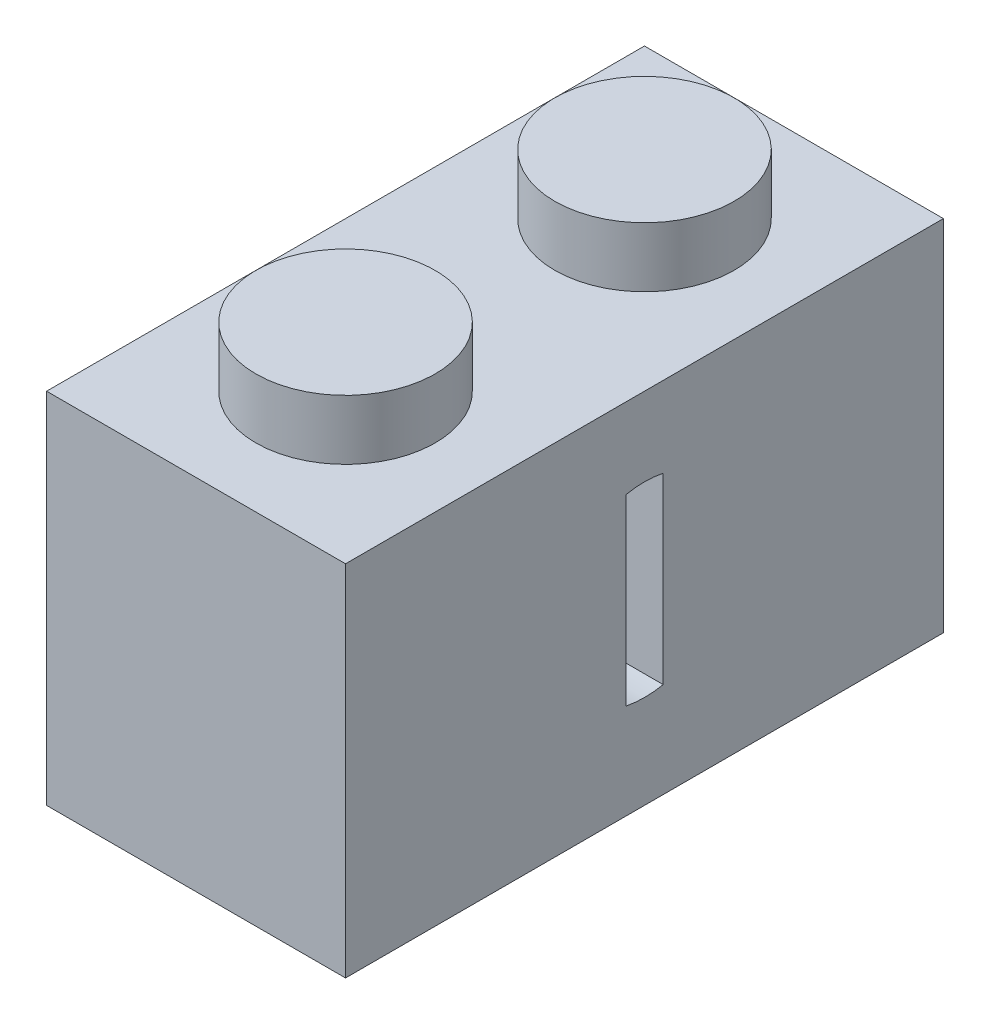
SolidWorks part; units mm, degrees
ref_plane "Front Plane" through (0, 0, 0) normal (0, 0, 1) x (1, 0, 0)
ref_plane "Top Plane" through (0, 0, 0) normal (0, 1, 0) x (1, 0, 0)
ref_plane "Right Plane" through (0, 0, 0) normal (1, 0, 0) x (0, 0, -1)
sketch "Sketch1" plane through (0, 0, 0) normal (0, 0, 1) x (1, 0, 0)
  line L1 (0, 9.6) -> (8, 9.6)
  line L2 (0, 9.6) -> (0, 0)
  line L3 (0, 0) -> (8, 0)
  line L4 (8, 9.6) -> (8, 0)
  dimension "D1" = 8
  dimension "D2" = 9.6
extrude "Boss-Extrude1" add sketch "Sketch1" along normal blind 16 contours L2 L1 L4 L3
sketch "Sketch4" plane through (0, 0, 0) normal (0, -1, 0) x (1, 0, 0)
  line L0 (1.6, 14.4) -> (1.6, 1.6)
  line L1 (1.6, 1.6) -> (6.4, 1.6)
  line L2 (6.4, 1.6) -> (6.4, 14.4)
  line L3 (6.4, 14.4) -> (1.6, 14.4)
  line L4 (0, 0) -> (8, 0)
  line L5 (8, 0) -> (8, 16)
  line L6 (8, 16) -> (0, 16)
  line L7 (0, 16) -> (0, 0)
  line L8 (0, 0) -> (8, 0)
  line L9 (8, 0) -> (8, 16)
  line L10 (8, 16) -> (0, 16)
  line L11 (0, 16) -> (0, 0)
  dimension "D1" = 0
  dimension "D2" = 1.6
extrude "Cut-Extrude1" cut sketch "Sketch4" against normal offset from surface (8 mm away) 8 contours L1 L2 L3 L0 up to face at (4, 0, 8)
sketch "Sketch5" plane through (0, 9.6, 0) normal (0, 1, 0) x (1, 0, 0)
  line L0 (4, -12) -> (4, -16) construction
  line L1 (0, -16) -> (8, -16) construction
  line L2 (4, -4) -> (4, 0) construction
  line L3 (0, 0) -> (8, 0) construction
  line L4 (0, -16) -> (0, 0) construction
  circle A0 centre (4, -12) radius 2.4
  circle A1 centre (4, -4) radius 2.4
  dimension "D1" = 4.8
  dimension "D2" = 0
  dimension "D3" = 8
extrude "Boss-Extrude2" add sketch "Sketch5" along normal blind 1.6 contours A0 | A1
sketch "Sketch6" plane through (6.4, 0, 0) normal (-1, 0, 0) x (0, 0, 1)
  line L0 (1.6, 5) -> (8, 5) construction
  line L1 (8, 5) -> (14.4, 5) construction
  line L4 (1.6, 8) -> (1.6, 0)
  line L5 (1.6, 0) -> (14.4, 0)
  line L6 (14.4, 0) -> (14.4, 8)
  line L7 (14.4, 8) -> (1.6, 8)
  line L8 (1.6, 8) -> (1.6, 0)
  line L9 (1.6, 0) -> (14.4, 0)
  line L10 (14.4, 0) -> (14.4, 8)
  line L11 (14.4, 8) -> (1.6, 8) construction
  circle A0 centre (8, 5) radius 3.5
  line M11 (14.4, 8) -> (1.6, 8)
  dimension "D2" = 7
  dimension "D3" = 3
  dimension "D1" = 0
extrude "Boss-Extrude3" add sketch "Sketch6" along normal up to surface (4.8 mm away) contours A0 M11 up to face at (1.6, 4, 8)
sketch "Sketch7" plane through (0, 0, 0) normal (-1, 0, 0) x (0, 0, 1)
  arc A0 (6.1972, 8) -> (9.8028, 8) centre (8, 5) ccw construction
  arc A1 (6.1972, 8) -> (9.8028, 8) centre (8, 5) ccw
  circle A2 centre (8, 5) radius 2.5
  dimension "D1" = 5
extrude "Cut-Extrude2" cut sketch "Sketch7" against normal blind 3.5 contours A2
sketch "Sketch8" plane through (3.5, 0, 0) normal (-1, 0, 0) x (0, 0, 1)
  line L0 (7.5, 7.4495) -> (7.5, 2.5505)
  line L1 (8.5, 7.4495) -> (8.5, 2.5505)
  line L2 (7.5, 5) -> (8, 5) construction
  circle A0 centre (8, 5) radius 2.5 construction
  circle A1 centre (8, 5) radius 2.5
  dimension "D1" = 1
  dimension "D2" = 0.5
extrude "Cut-Extrude3" cut sketch "Sketch8" against normal up to surface (4.5 mm away)
sketch "Sketch9" plane through (0, 0, 0) normal (-1, 0, 0) x (0, 0, 1)
  circle A0 centre (8, 5) radius 2.5 construction
  circle A1 centre (8, 5) radius 2.5
  circle A2 centre (8, 5) radius 3.25
  dimension "D1" = 0.75
extrude "Boss-Extrude4" add sketch "Sketch9" along normal blind 1.6
ref_plane "Plane1" through (0, 8.25, 0) normal (0, 1, 0) x (1, 0, 0)
sketch "Sketch10" plane through (0, 8.25, 0) normal (0, 1, 0) x (1, 0, 0)
  line L0 (-1.6, -4.75) -> (-1.6, -11.25) construction
  line L1 (-1.6, -4.75) -> (-1.6, -11.25)
  line L2 (-1.6, -11.25) -> (0, -11.25)
  line L3 (-1.6, -4.75) -> (0, -4.75)
  line L6 (8, 0) -> (0, 0)
  line L7 (0, 0) -> (0, -16)
  line L8 (0, -16) -> (8, -16)
  line L9 (8, -16) -> (8, 0)
  line L10 (8, 0) -> (0, 0)
  line L11 (0, 0) -> (0, -16)
  line L12 (0, -16) -> (8, -16)
  line L13 (8, -16) -> (8, 0)
  dimension "D1" = 0
extrude "Cut-Extrude4" cut sketch "Sketch10" against normal blind 1 contours L11 L3 L1 L2
